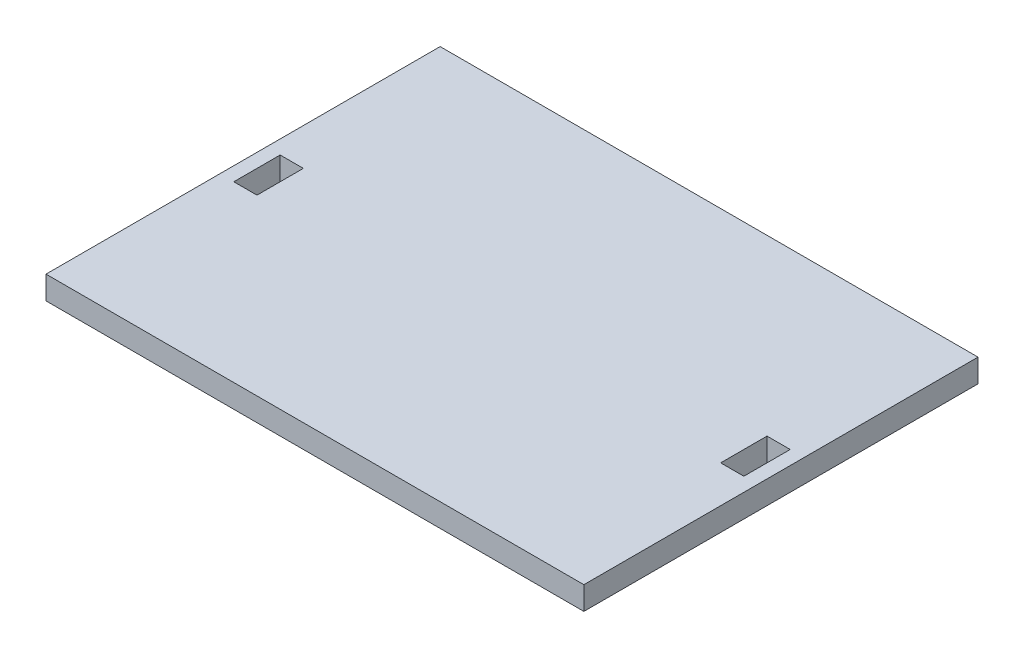
SolidWorks part; units mm, degrees
ref_plane "Front Plane" through (0, 0, 0) normal (0, 0, 1) x (1, 0, 0)
ref_plane "Top Plane" through (0, 0, 0) normal (0, 1, 0) x (1, 0, 0)
ref_plane "Right Plane" through (0, 0, 0) normal (1, 0, 0) x (0, 0, -1)
sketch "Sketch1" plane through (0, 0, 0) normal (0, 1, 0) x (1, 0, 0)
  line L1 (-58, -42.5) -> (58, -42.5)
  line L2 (-58, -42.5) -> (-58, 42.5)
  line L3 (-58, 42.5) -> (58, 42.5)
  line L4 (58, -42.5) -> (58, 42.5)
  line L5 (-58, -42.5) -> (58, 42.5) construction
  line L6 (-58, 42.5) -> (58, -42.5) construction
  point P0 (0, 0)
  dimension "D1" = 116
  dimension "D2" = 85
extrude "Boss-Extrude1" add sketch "Sketch1" along normal blind 5
sketch "Sketch3" plane through (0, 5, 0) normal (0, 1, 0) x (1, 0, 0)
  line L0 (-58, 42.5) -> (-58, -42.5) construction
  line L1 (-55, 5) -> (-50, 5)
  line L2 (-55, 5) -> (-55, -5)
  line L3 (-55, -5) -> (-50, -5)
  line L4 (-50, 5) -> (-50, -5)
  line L5 (0, 0) -> (0, 11.4585) construction
  line L6 (50, 5) -> (50, -5)
  line L7 (55, 5) -> (50, 5)
  line L8 (55, 5) -> (55, -5)
  line L9 (55, -5) -> (50, -5)
  dimension "D1" = 10
  dimension "D2" = 5
  dimension "D3" = 37.5
  dimension "D4" = 3
extrude "Cut-Extrude1" cut sketch "Sketch3" against normal blind 10
